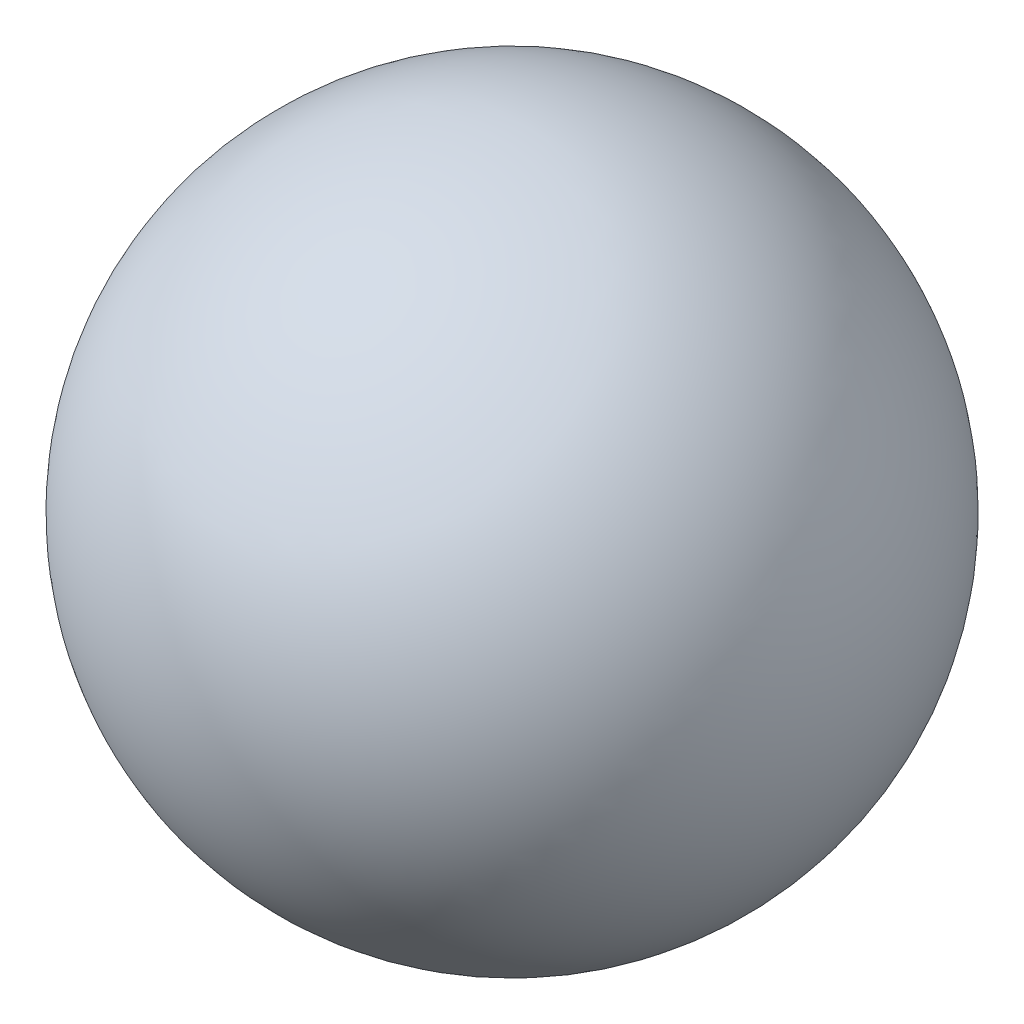
SolidWorks part; units mm, degrees
material "Titanium"
ref_plane "Front Plane" through (0, 0, 0) normal (0, 0, 1) x (1, 0, 0)
ref_plane "Top Plane" through (0, 0, 0) normal (0, 1, 0) x (1, 0, 0)
ref_plane "Right Plane" through (0, 0, 0) normal (1, 0, 0) x (0, 0, -1)
sketch "Sketch1" plane through (0, 0, 0) normal (0, 1, 0) x (1, 0, 0)
  line L0 (0, 0) -> (0, 500)
  arc A0 (0, 500) -> (0, 0) centre (0, 250) cw
  dimension "D1" = 500
revolve "Revolve1" add sketch "Sketch1" angle 360 about L0
